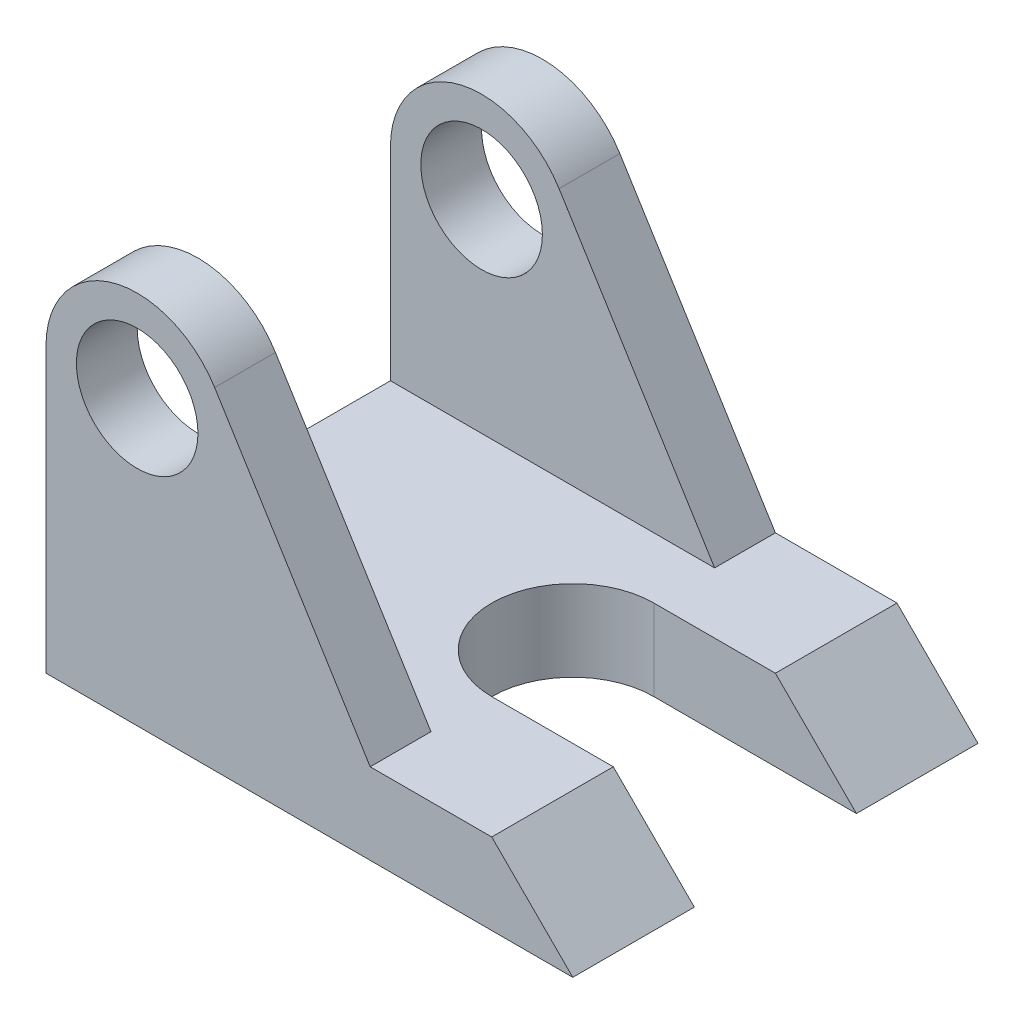
SolidWorks part; units mm, degrees
ref_plane "Front Plane" through (0, 0, 0) normal (0, 0, 1) x (1, 0, 0)
ref_plane "Top Plane" through (0, 0, 0) normal (0, 1, 0) x (1, 0, 0)
ref_plane "Right Plane" through (0, 0, 0) normal (1, 0, 0) x (0, 0, -1)
sketch "Sketch1" plane through (0, 0, 0) normal (0, 0, 1) x (1, 0, 0)
  line L0 (0, 0) -> (0, 70)
  line L3 (130, 0) -> (0, 0)
  line L4 (41.6192, 81.862) -> (80, 20)
  line L5 (80, 20) -> (110, 20)
  line L6 (110, 20) -> (130, 0)
  circle A0 centre (22.5, 70) radius 22.5
  circle A1 centre (22.5, 70) radius 15
  point P1 (110, 20)
  point P3 (80, 20)
  point P11 (0, 0)
  point P12 (0, 0)
  point P14 (0, 0)
  dimension "D3" = 45
  dimension "D4" = 30
  dimension "D5" = 20
  dimension "D1" = 70
  dimension "D2" = 130
  dimension "D6" = 30
  dimension "D7" = 20
extrude "Boss-Extrude1" add sketch "Sketch1" against normal blind 100 contours A0 L0 L3 L6 L5 L4 | A0 A1
sketch "Sketch2" plane through (0, 20, 0) normal (0, 1, 0) x (1, 0, 0)
  line L0 (41.6192, 100) -> (80, 100) construction
  line L1 (-19.0977, 85) -> (148.1095, 85)
  line L2 (-19.0977, 85) -> (-19.0977, 15)
  line L3 (-19.0977, 15) -> (148.1095, 15)
  line L4 (148.1095, 85) -> (148.1095, 15)
  line L5 (41.6192, 0) -> (80, 0) construction
  dimension "D1" = 15
  dimension "D2" = 15
extrude "Cut-Extrude1" cut sketch "Sketch2" along normal through all
sketch "Sketch3" plane through (0, 20, 0) normal (0, 1, 0) x (1, 0, 0)
  line L0 (130, 100) -> (130, 0) construction
  line L2 (80, 0) -> (110, 0) construction
  line L3 (80, 70) -> (130, 70)
  line L4 (130, 70) -> (130, 30)
  line L5 (130, 30) -> (80, 30)
  arc A0 (80, 70) -> (80, 30) centre (80, 50) ccw
  dimension "D1" = 40
  dimension "D2" = 50
  dimension "D3" = 50
extrude "Cut-Extrude2" cut sketch "Sketch3" against normal through all
